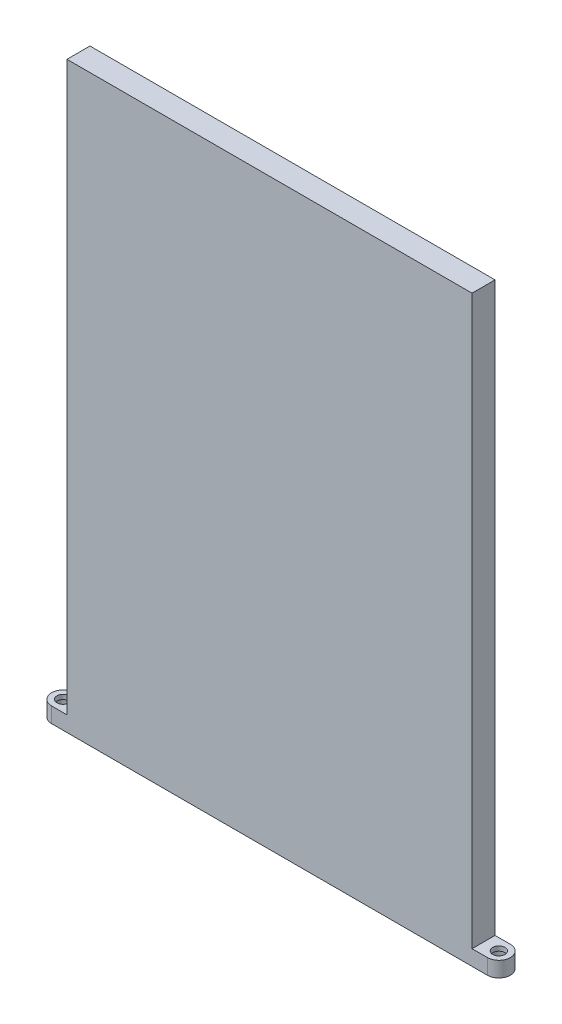
SolidWorks part; units mm, degrees
ref_plane "Front Plane" through (0, 0, 0) normal (0, 0, 1) x (1, 0, 0)
ref_plane "Top Plane" through (0, 0, 0) normal (0, 1, 0) x (1, 0, 0)
ref_plane "Right Plane" through (0, 0, 0) normal (1, 0, 0) x (0, 0, -1)
sketch "Sketch1" plane through (0, 0, 0) normal (0, 0, 1) x (1, 0, 0)
  line L1 (66, -95) -> (-66, -95)
  line L2 (66, -95) -> (66, 95)
  line L3 (66, 95) -> (-66, 95)
  line L4 (-66, -95) -> (-66, 95)
  line L5 (66, -95) -> (-66, 95) construction
  line L6 (66, 95) -> (-66, -95) construction
  point P0 (0, 0)
  dimension "D1" = 190
  dimension "D2" = 132
extrude "Boss-Extrude1" add sketch "Sketch1" along normal blind 7.5
sketch "Sketch2" plane through (0, -95, 0) normal (0, -1, 0) x (-1, 0, 0)
  line L1 (66, -7.5) -> (71, -7.5)
  line L2 (66, -7.5) -> (66, 0)
  line L3 (66, 0) -> (71, 0)
  line L4 (71, -7.5) -> (71, 0)
  line L5 (-66, -7.5) -> (-71, -7.5)
  line L6 (-66, -7.5) -> (-66, 0)
  line L7 (-66, 0) -> (-71, 0)
  line L8 (-71, -7.5) -> (-71, 0)
  arc A0 (71, 0) -> (71, -7.5) centre (71, -3.75) cw
  arc A1 (-71, -7.5) -> (-71, 0) centre (-71, -3.75) cw
  point P14 (0, 0)
  line M6 (-66, 0) -> (-66, -7.5)
  line M8 (66, -7.5) -> (66, 0)
  dimension "D1" = 5
  dimension "D2" = 5
  dimension "D3" = 7.5
  dimension "D4" = 7.5
extrude "Boss-Extrude2" add sketch "Sketch2" against normal blind 5 contours A0 L4 | L1 L4 L3 M8 | A1 L8 | L8 L5 L7 M6
sketch "Sketch3" plane through (0, -95, 0) normal (0, -1, 0) x (-1, 0, 0)
  line L1 (71, -7.5) -> (-71, -7.5) construction
  circle A0 centre (71, -3.75) radius 2
  circle A1 centre (-71, -3.75) radius 2
  point P5 (0, 0)
  dimension "D1" = 4
  dimension "D2" = 4
  dimension "D3" = 142
  dimension "D4" = 3.75
extrude "Cut-Extrude1" cut sketch "Sketch3" against normal blind 5
sketch "Sketch4" plane through (0, -95, 0) normal (0, -1, 0) x (-1, 0, 0)
  line L0 (0, -34.2045) -> (0, 35.6714) construction
  circle A0 centre (71, -3.75) radius 3
  circle A1 centre (-71, -3.75) radius 3
  dimension "D1" = 6
extrude "Cut-Extrude2" cut sketch "Sketch4" against normal blind 3.5
